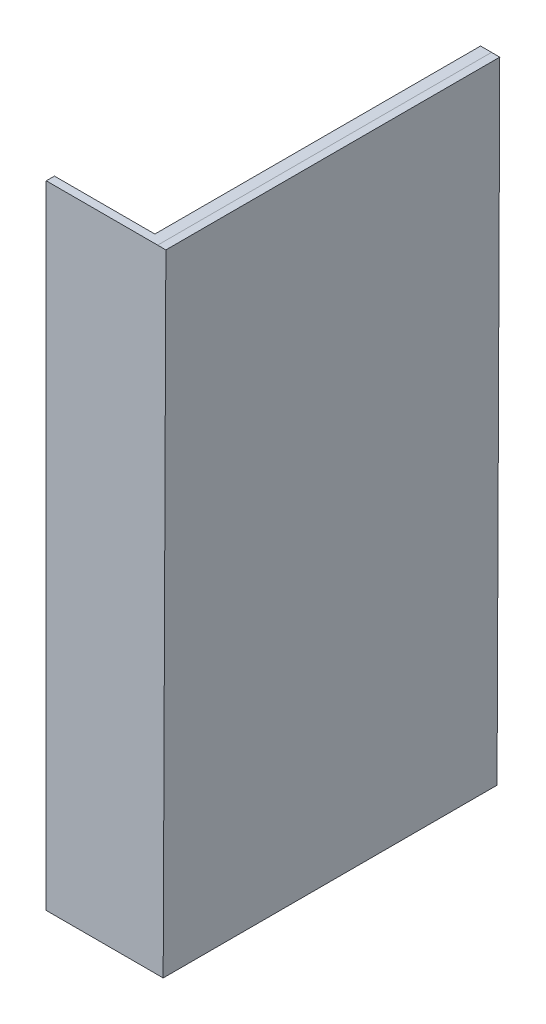
SolidWorks part; units mm, degrees
ref_plane "Front Plane" through (0, 0, 0) normal (0, 0, 1) x (1, 0, 0)
ref_plane "Top Plane" through (0, 0, 0) normal (0, 1, 0) x (1, 0, 0)
ref_plane "Right Plane" through (0, 0, 0) normal (1, 0, 0) x (0, 0, -1)
sketch "Sketch1" plane through (0, 0, 0) normal (0, 0, 1) x (1, 0, 0)
  line L0 (-1606.8414, 1223.6975) -> (429.5102, 1223.6975)
  line L3 (380.2634, -10326.4647) -> (-1606.8414, -10326.4647)
  line L4 (-1606.8414, 1223.6975) -> (-1606.8414, -10326.4647)
  line L5 (429.5102, 1223.6975) -> (380.2634, -10326.4647)
extrude "Boss-Extrude1" add sketch "Sketch1" along normal blind 150
sketch "Sketch2" plane through (424.285, -1.809, 0) normal (1, -0.0043, 0) x (0, 0, -1)
  line L4 (0, -10324.7495) -> (0, 1225.5177)
  line L5 (0, 1225.5177) -> (-150, 1225.5177)
  line L6 (-150, 1225.5177) -> (-150, -10324.7495)
  line L7 (-150, -10324.7495) -> (0, -10324.7495)
  line L8 (0, -10324.7495) -> (0, 1225.5177)
  line L9 (0, 1225.5177) -> (-150, 1225.5177)
  line L10 (-150, 1225.5177) -> (-150, -10324.7495)
  line L11 (-150, -10324.7495) -> (0, -10324.7495)
  dimension "D1" = 0
extrude "Boss-Extrude2" add sketch "Sketch2" along normal blind 150
sketch "Sketch3" plane through (0, 0, 0) normal (0, 0, -1) x (-1, 0, 0)
  line L0 (-228.3644, -10326.4647) -> (-228.3644, 1223.6975)
  line L6 (1606.8414, 1223.6975) -> (-429.5102, 1223.6975)
  line L7 (-429.5102, 1223.6975) -> (-579.5089, 1223.058)
  line L8 (-579.5089, 1223.058) -> (-530.262, -10327.1042)
  line L9 (-530.262, -10327.1042) -> (-380.2634, -10326.4647)
  line L10 (-380.2634, -10326.4647) -> (1606.8414, -10326.4647)
  line L11 (1606.8414, -10326.4647) -> (1606.8414, 1223.6975)
  line L12 (-228.3644, 1223.6975) -> (-429.5102, 1223.6975)
  line L13 (-429.5102, 1223.6975) -> (-579.5089, 1223.058)
  line L14 (-579.5089, 1223.058) -> (-530.262, -10327.1042)
  line L15 (-530.262, -10327.1042) -> (-380.2634, -10326.4647)
  line L16 (-380.2634, -10326.4647) -> (-228.3644, -10326.4647)
  dimension "D1" = 0
extrude "Boss-Extrude3" add sketch "Sketch3" along normal blind 5953 contours L12 L13 L14 L15 L16 L0
